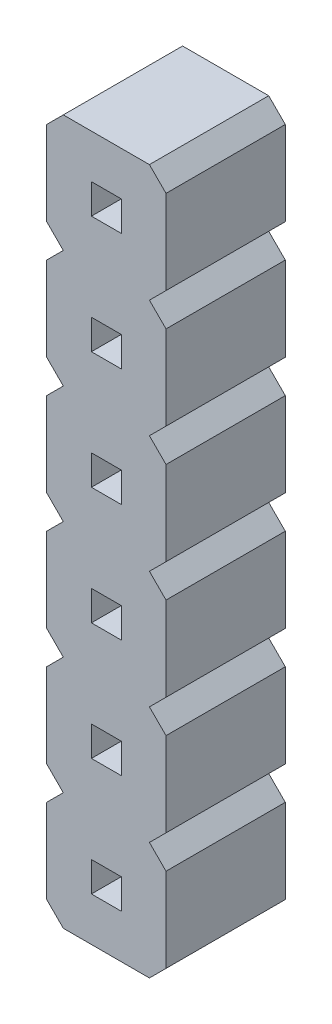
SolidWorks part; units mm, degrees
ref_plane "Alzado" through (0, 0, 0) normal (0, 0, 1) x (1, 0, 0)
ref_plane "Planta" through (0, 0, 0) normal (0, 1, 0) x (1, 0, 0)
ref_plane "Vista lateral" through (0, 0, 0) normal (1, 0, 0) x (0, 0, -1)
sketch "pin_body" plane through (0, 0, 0) normal (0, 0, 1) x (1, 0, 0)
  line L0 (0.9525, -0.932) -> (0, -0.932) construction
  line L1 (0, 2.1464) -> (0, 0.3536)
  line L2 (0, -0.3536) -> (0, -2.1464)
  line L3 (0, -0.3536) -> (0.3536, 0)
  line L4 (1.5885, -1.568) -> (2.541, -1.568) construction
  line L5 (0, 2.1464) -> (0.3536, 2.5)
  line L6 (2.541, -0.3536) -> (2.541, -2.1464)
  line L7 (0.9525, -1.25) -> (0.9525, -0.932) construction
  line L8 (2.541, -2.1464) -> (2.1874, -2.5)
  line L9 (2.1874, 0) -> (2.541, -0.3536)
  line L10 (1.5885, -1.25) -> (1.5885, -1.568) construction
  line L11 (0.3536, -2.5) -> (0, -2.1464)
  line L12 (0.9525, -0.932) -> (1.5885, -0.932)
  line L13 (0.9525, -0.932) -> (0.9525, -1.568)
  line L14 (0.9525, -1.568) -> (1.5885, -1.568)
  line L15 (1.5885, -0.932) -> (1.5885, -1.568)
  line L16 (2.541, 2.1464) -> (2.541, 0.3536)
  line L17 (2.541, 0.3536) -> (2.1874, 0)
  line L18 (2.1874, 2.5) -> (2.541, 2.1464)
  line L19 (0.3536, 0) -> (0, 0.3536)
  line L20 (0.9525, 1.568) -> (1.5885, 1.568)
  line L21 (0.9525, 1.568) -> (0.9525, 0.932)
  line L22 (0.9525, 0.932) -> (1.5885, 0.932)
  line L23 (1.5885, 1.568) -> (1.5885, 0.932)
  line L24 (0.9525, 1.568) -> (0, 1.568) construction
  line L25 (1.5885, 0.932) -> (2.541, 0.932) construction
  line L26 (0.9525, 1.25) -> (0.9525, 1.568) construction
  line L27 (1.5885, 1.25) -> (1.5885, 0.932) construction
  line L28 (0, 4.6464) -> (0, 2.8536)
  line L29 (0, 4.6464) -> (0.3536, 5)
  line L30 (2.541, 4.6464) -> (2.541, 2.8536)
  line L31 (2.541, 2.8536) -> (2.1874, 2.5)
  line L32 (2.1874, 5) -> (2.541, 4.6464)
  line L33 (0.3536, 2.5) -> (0, 2.8536)
  line L34 (0.9525, 4.068) -> (1.5885, 4.068)
  line L35 (0.9525, 4.068) -> (0.9525, 3.432)
  line L36 (0.9525, 3.432) -> (1.5885, 3.432)
  line L37 (1.5885, 4.068) -> (1.5885, 3.432)
  line L38 (0.9525, 4.068) -> (0, 4.068) construction
  line L39 (1.5885, 3.432) -> (2.541, 3.432) construction
  line L40 (0.9525, 3.75) -> (0.9525, 4.068) construction
  line L41 (1.5885, 3.75) -> (1.5885, 3.432) construction
  line L42 (0, 7.1464) -> (0, 5.3536)
  line L43 (0, 7.1464) -> (0.3536, 7.5)
  line L44 (2.541, 7.1464) -> (2.541, 5.3536)
  line L45 (2.541, 5.3536) -> (2.1874, 5)
  line L46 (2.1874, 7.5) -> (2.541, 7.1464)
  line L47 (0.3536, 5) -> (0, 5.3536)
  line L48 (0.9525, 6.568) -> (1.5885, 6.568)
  line L49 (0.9525, 6.568) -> (0.9525, 5.932)
  line L50 (0.9525, 5.932) -> (1.5885, 5.932)
  line L51 (1.5885, 6.568) -> (1.5885, 5.932)
  line L52 (0.9525, 6.568) -> (0, 6.568) construction
  line L53 (1.5885, 5.932) -> (2.541, 5.932) construction
  line L54 (0.9525, 6.25) -> (0.9525, 6.568) construction
  line L55 (1.5885, 6.25) -> (1.5885, 5.932) construction
  line L56 (0, 9.6464) -> (0, 7.8536)
  line L57 (0, 9.6464) -> (0.3536, 10)
  line L58 (2.541, 9.6464) -> (2.541, 7.8536)
  line L59 (2.541, 7.8536) -> (2.1874, 7.5)
  line L60 (2.1874, 10) -> (2.541, 9.6464)
  line L61 (0.3536, 7.5) -> (0, 7.8536)
  line L62 (0.9525, 9.068) -> (1.5885, 9.068)
  line L63 (0.9525, 9.068) -> (0.9525, 8.432)
  line L64 (0.9525, 8.432) -> (1.5885, 8.432)
  line L65 (1.5885, 9.068) -> (1.5885, 8.432)
  line L66 (0.9525, 9.068) -> (0, 9.068) construction
  line L67 (1.5885, 8.432) -> (2.541, 8.432) construction
  line L68 (0.9525, 8.75) -> (0.9525, 9.068) construction
  line L69 (1.5885, 8.75) -> (1.5885, 8.432) construction
  line L70 (0, 12.1464) -> (0, 10.3536)
  line L71 (0, 12.1464) -> (0.3536, 12.5)
  line L72 (2.541, 12.1464) -> (2.541, 10.3536)
  line L73 (2.541, 10.3536) -> (2.1874, 10)
  line L74 (2.1874, 12.5) -> (2.541, 12.1464)
  line L75 (0.3536, 10) -> (0, 10.3536)
  line L76 (0.9525, 11.568) -> (1.5885, 11.568)
  line L77 (0.9525, 11.568) -> (0.9525, 10.932)
  line L78 (0.9525, 10.932) -> (1.5885, 10.932)
  line L79 (1.5885, 11.568) -> (1.5885, 10.932)
  line L80 (0.9525, 11.568) -> (0, 11.568) construction
  line L81 (1.5885, 10.932) -> (2.541, 10.932) construction
  line L82 (0.9525, 11.25) -> (0.9525, 11.568) construction
  line L83 (1.5885, 11.25) -> (1.5885, 10.932) construction
  line L84 (0.3536, 12.5) -> (2.1874, 12.5)
  line L168 (2.1874, -2.5) -> (0.3536, -2.5)
  line L170 (0, 17.1464) -> (0, 15.3536) [skipped]
  line L171 (0, 17.1464) -> (0.3536, 17.5) [skipped]
  line L172 (2.541, 17.1464) -> (2.541, 15.3536) [skipped]
  line L173 (2.541, 15.3536) -> (2.1874, 15) [skipped]
  line L174 (2.1874, 17.5) -> (2.541, 17.1464) [skipped]
  line L175 (0.9525, 16.568) -> (1.5885, 16.568) [skipped]
  line L176 (0.9525, 16.568) -> (0.9525, 15.932) [skipped]
  line L177 (0.9525, 15.932) -> (1.5885, 15.932) [skipped]
  line L178 (1.5885, 16.568) -> (1.5885, 15.932) [skipped]
  line L179 (0, 19.6464) -> (0, 17.8536) [skipped]
  line L180 (0, 19.6464) -> (0.3536, 20) [skipped]
  line L181 (2.541, 19.6464) -> (2.541, 17.8536) [skipped]
  line L182 (2.541, 17.8536) -> (2.1874, 17.5) [skipped]
  line L183 (2.1874, 20) -> (2.541, 19.6464) [skipped]
  line L184 (0.3536, 17.5) -> (0, 17.8536) [skipped]
  line L185 (0.9525, 19.068) -> (1.5885, 19.068) [skipped]
  line L186 (0.9525, 19.068) -> (0.9525, 18.432) [skipped]
  line L187 (0.9525, 18.432) -> (1.5885, 18.432) [skipped]
  line L188 (1.5885, 19.068) -> (1.5885, 18.432) [skipped]
  line L189 (0, 22.1464) -> (0, 20.3536) [skipped]
  line L190 (0, 22.1464) -> (0.3536, 22.5) [skipped]
  line L191 (2.541, 22.1464) -> (2.541, 20.3536) [skipped]
  line L192 (2.541, 20.3536) -> (2.1874, 20) [skipped]
  line L193 (2.1874, 22.5) -> (2.541, 22.1464) [skipped]
  line L194 (0.3536, 20) -> (0, 20.3536) [skipped]
  line L195 (0.9525, 21.568) -> (1.5885, 21.568) [skipped]
  line L196 (0.9525, 21.568) -> (0.9525, 20.932) [skipped]
  line L197 (0.9525, 20.932) -> (1.5885, 20.932) [skipped]
  line L198 (1.5885, 21.568) -> (1.5885, 20.932) [skipped]
  line L199 (0, 24.6464) -> (0, 22.8536) [skipped]
  line L200 (0, 24.6464) -> (0.3536, 25) [skipped]
  line L201 (2.541, 24.6464) -> (2.541, 22.8536) [skipped]
  line L202 (2.541, 22.8536) -> (2.1874, 22.5) [skipped]
  line L203 (2.1874, 25) -> (2.541, 24.6464) [skipped]
  line L204 (0.3536, 22.5) -> (0, 22.8536) [skipped]
  line L205 (0.9525, 24.068) -> (1.5885, 24.068) [skipped]
  line L206 (0.9525, 24.068) -> (0.9525, 23.432) [skipped]
  line L207 (0.9525, 23.432) -> (1.5885, 23.432) [skipped]
  line L208 (1.5885, 24.068) -> (1.5885, 23.432) [skipped]
  line L209 (0, 27.1464) -> (0, 25.3536) [skipped]
  line L210 (0, 27.1464) -> (0.3536, 27.5) [skipped]
  line L211 (2.541, 27.1464) -> (2.541, 25.3536) [skipped]
  line L212 (2.541, 25.3536) -> (2.1874, 25) [skipped]
  line L213 (2.1874, 27.5) -> (2.541, 27.1464) [skipped]
  line L214 (0.3536, 25) -> (0, 25.3536) [skipped]
  line L215 (0.9525, 26.568) -> (1.5885, 26.568) [skipped]
  line L216 (0.9525, 26.568) -> (0.9525, 25.932) [skipped]
  line L217 (0.9525, 25.932) -> (1.5885, 25.932) [skipped]
  line L218 (1.5885, 26.568) -> (1.5885, 25.932) [skipped]
  line L219 (0.9525, 16.568) -> (0, 16.568) construction
  line L220 (1.5885, 15.932) -> (2.541, 15.932) construction
  line L221 (0.9525, 16.25) -> (0.9525, 16.568) construction
  line L222 (1.5885, 16.25) -> (1.5885, 15.932) construction
  line L223 (0.9525, 19.068) -> (0, 19.068) construction
  line L224 (1.5885, 18.432) -> (2.541, 18.432) construction
  line L225 (0.9525, 18.75) -> (0.9525, 19.068) construction
  line L226 (1.5885, 18.75) -> (1.5885, 18.432) construction
  line L227 (0.9525, 21.568) -> (0, 21.568) construction
  line L228 (1.5885, 20.932) -> (2.541, 20.932) construction
  line L229 (0.9525, 21.25) -> (0.9525, 21.568) construction
  line L230 (1.5885, 21.25) -> (1.5885, 20.932) construction
  line L231 (0.9525, 24.068) -> (0, 24.068) construction
  line L232 (1.5885, 23.432) -> (2.541, 23.432) construction
  line L233 (0.9525, 23.75) -> (0.9525, 24.068) construction
  line L234 (1.5885, 23.75) -> (1.5885, 23.432) construction
  line L235 (0.9525, 26.568) -> (0, 26.568) construction
  line L236 (1.5885, 25.932) -> (2.541, 25.932) construction
  line L237 (0.9525, 26.25) -> (0.9525, 26.568) construction
  line L238 (1.5885, 26.25) -> (1.5885, 25.932) construction
  line L239 (0, 14.6464) -> (0.3536, 15) [skipped]
  line L240 (2.1874, 15) -> (2.541, 14.6464) [skipped]
  line L241 (0.9525, 14.068) -> (1.5885, 14.068) [skipped]
  line L242 (0.9525, 14.068) -> (0.9525, 13.432) [skipped]
  line L243 (0.9525, 13.432) -> (1.5885, 13.432) [skipped]
  line L244 (1.5885, 14.068) -> (1.5885, 13.432) [skipped]
  line L245 (0.3536, 15) -> (0, 15.3536) [skipped]
  line L246 (0.9525, 14.068) -> (0, 14.068) construction
  line L247 (0.9525, 13.75) -> (0.9525, 14.068) construction
  line L248 (1.5885, 13.75) -> (1.5885, 13.432) construction
  line L249 (2.541, 14.6464) -> (2.541, 12.8536) [skipped]
  line L250 (2.541, 12.8536) -> (2.1874, 12.5) [skipped]
  line L251 (1.5885, 13.432) -> (2.541, 13.432) construction
  line L252 (0, 14.6464) -> (0, 12.8536) [skipped]
  line L253 (0.3536, 12.5) -> (0, 12.8536) [skipped]
  dimension "D1" = 0.318
  dimension "D2" = 0.9525
  dimension "D3" = 0.5
  dimension "D4" = 135
  dimension "D5" = 0.5
  dimension "D6" = 135
  dimension "D7" = 12
extrude "Boss-Extrude1" add sketch "pin_body" along normal blind 2.54
